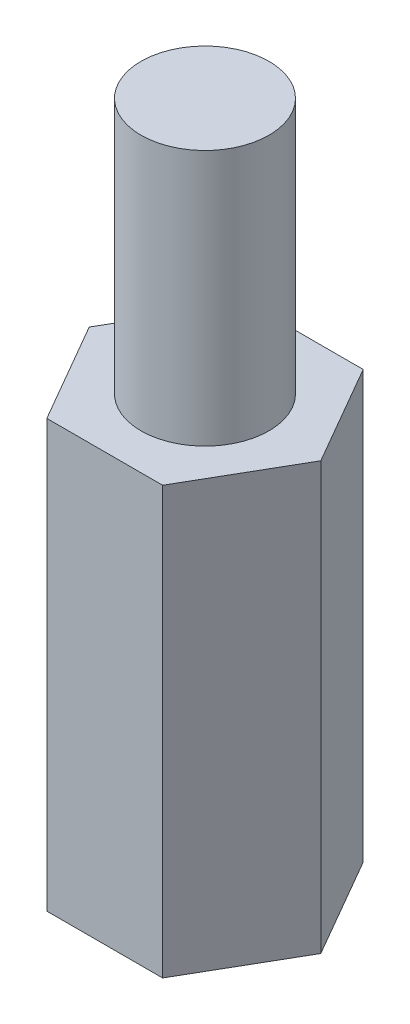
SolidWorks part; units mm, degrees
ref_plane "前视基准面" through (0, 0, 0) normal (0, 0, 1) x (1, 0, 0)
ref_plane "上视基准面" through (0, 0, 0) normal (0, 1, 0) x (1, 0, 0)
ref_plane "右视基准面" through (0, 0, 0) normal (1, 0, 0) x (0, 0, -1)
sketch "草图1" plane through (0, 0, 0) normal (0, 1, 0) x (1, 0, 0)
  line L1 (1.3568, 2.35) -> (-1.3568, 2.35)
  line L2 (-1.3568, 2.35) -> (-2.7135, 0)
  line L3 (-2.7135, 0) -> (-1.3568, -2.35)
  line L4 (-1.3568, -2.35) -> (1.3568, -2.35)
  line L5 (1.3568, -2.35) -> (2.7135, 0)
  line L6 (2.7135, 0) -> (1.3568, 2.35)
  circle A0 centre (0, 0) radius 2.35 construction
  dimension "D1" = 4.7
extrude "凸台-拉伸1" add sketch "草图1" along normal blind 10
sketch "草图2" plane through (0, 10, 0) normal (0, 1, 0) x (1, 0, 0)
  circle A0 centre (0, 0) radius 1.5
  dimension "D1" = 3
extrude "凸台-拉伸2" add sketch "草图2" along normal blind 6
sketch "草图3" plane through (0, 0, 0) normal (0, -1, 0) x (1, 0, 0)
  circle A0 centre (0, 0) radius 1.5
  dimension "D1" = 3
extrude "切除-拉伸1" cut sketch "草图3" against normal blind 7
sketch "草图4" plane through (0, 0, 0) normal (0, -1, 0) x (1, 0, 0)
  line L6 (1.3568, -2.35) -> (2.7135, 0)
  line L7 (2.7135, 0) -> (1.3568, 2.35)
  line L8 (1.3568, 2.35) -> (-1.3568, 2.35)
  line L9 (-1.3568, 2.35) -> (-2.7135, 0)
  line L10 (-2.7135, 0) -> (-1.3568, -2.35)
  line L11 (-1.3568, -2.35) -> (1.3568, -2.35)
  line L12 (1.3568, -2.35) -> (2.7135, 0)
  line L13 (2.7135, 0) -> (1.3568, 2.35)
  line L14 (1.3568, 2.35) -> (-1.3568, 2.35)
  line L15 (-1.3568, 2.35) -> (-2.7135, 0)
  line L16 (-2.7135, 0) -> (-1.3568, -2.35)
  line L17 (-1.3568, -2.35) -> (1.3568, -2.35)
  dimension "D1" = 0
